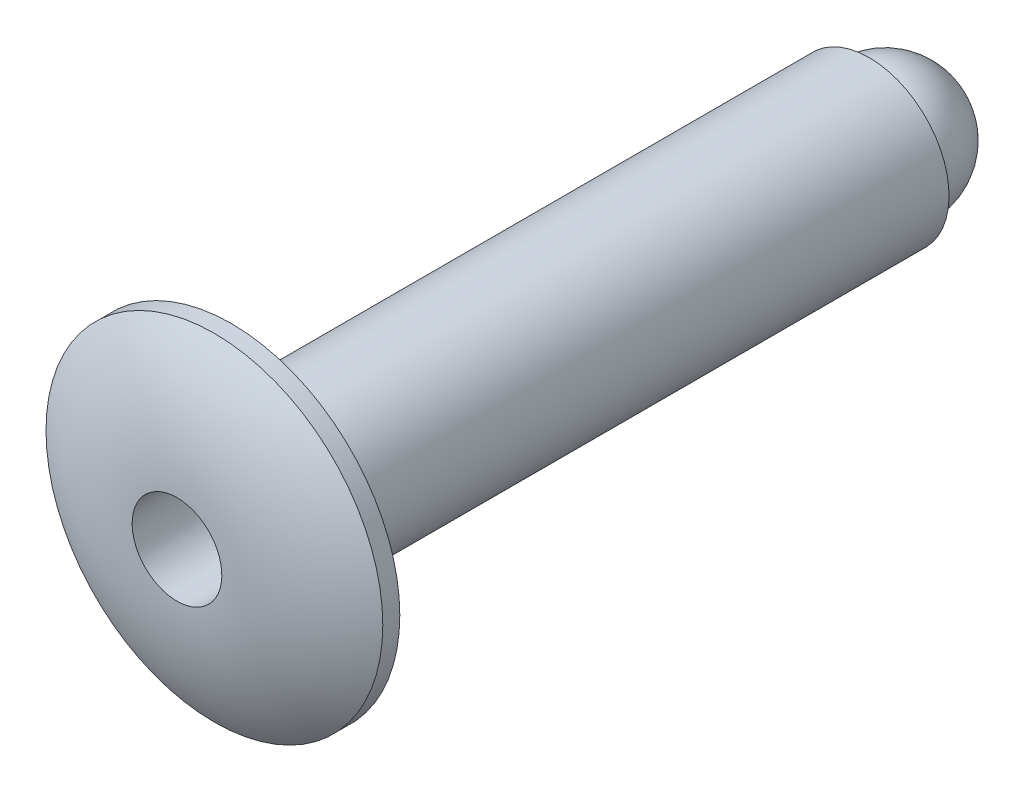
SolidWorks part; units mm, degrees
ref_plane "Front" through (0, 0, 0) normal (0, 0, 1) x (1, 0, 0)
ref_plane "Top" through (0, 0, 0) normal (0, 1, 0) x (1, 0, 0)
ref_plane "Right" through (0, 0, 0) normal (1, 0, 0) x (0, 0, -1)
sketch "Sketch1" plane through (0, 0, 0) normal (1, 0, 0) x (0, 0, -1)
  line L0 (-15.1003, 0) -> (-0.8128, 0) construction
  line L1 (-0.8128, 0) -> (0, 0) construction
  line L2 (0, 0) -> (9.525, 0) construction
  line L3 (9.525, 0) -> (10.7442, 0) construction
  line L8 (0, 2.5146) -> (0, -2.5146) construction
  line L9 (9.525, 1.1906) -> (9.525, -1.1906) construction
  dimension "Length" = 9.525
  dimension "Head Height" = 0.8128
  dimension "D5" = 1.2192
  dimension "D9" = 14.2875
  dimension "Diameter" = 2.3813
  dimension "Head Diameter" = 5.0292
sketch "Sketch2" plane through (0, 0, 0) normal (1, 0, 0) x (0, 0, -1)
  line L0 (-15.1003, 0.5953) -> (-15.1003, 0) construction
  line L1 (-15.1003, 0.5953) -> (0, 0.5953) construction
  line L2 (0, 2.5146) -> (0, -2.5146) construction
  line L3 (0, 0) -> (0, 2.5146) construction
  line L4 (-0.8128, 0) -> (-0.8128, -1.8472) construction
  line L5 (9.525, 1.1906) -> (0, 1.1906)
  line L6 (9.525, 1.1906) -> (9.525, 0) construction
  line L7 (10.7442, 0) -> (10.7442, 1.1906) construction
  line L8 (9.525, 1.1906) -> (9.525, 0)
  line L9 (10.7442, 1.1906) -> (9.525, 1.1906) construction
  line L11 (9.525, 0) -> (10.7442, 0) construction
  line L12 (9.525, 0) -> (0.9525, 0)
  line L13 (-0.8128, 0.5953) -> (-0.8128, 0) construction
  line L14 (9.525, 1.1906) -> (9.525, 0) construction
  line L15 (9.525, 1.1906) -> (9.525, 0) construction
  line L16 (9.525, 0) -> (9.525, 1.1906) construction
  line L17 (9.525, 1.1906) -> (9.525, 0) construction
  line L18 (9.525, 0) -> (9.525, 1.1906) construction
  line L19 (0, 1.1906) -> (0, 2.5146)
  line L20 (-0.8128, 0.6697) -> (0, 0.6697)
  line L21 (-15.1003, 0.6697) -> (0, 0.6697) construction
  line L22 (0, 2.5146) -> (-0.254, 2.5146)
  line L23 (0, 0.6697) -> (0.9525, 0.6697)
  line L24 (0.9525, 0.6697) -> (0.9525, 0)
  arc A0 (10.7442, 0) -> (9.525, 0.9525) centre (9.7625, 0) ccw construction
  arc A2 (-0.254, 2.5146) -> (-0.8128, 0.6697) centre (2.512, 0.6697) ccw
  dimension "D3" = 0.254
  dimension "D1" = 0.5953
  dimension "D2" = 0.9525
  dimension "D5" = 0.9525
  dimension "D4" = 0.0744
revolve "Revolve1" add sketch "Sketch2" angle 360 about L12
sketch "Sketch7" plane through (0, 0, 0) normal (1, 0, 0) x (0, 0, -1)
  line L0 (-15.1003, 0.5953) -> (0.9525, 0.5953)
  line L1 (0.9525, 0.6697) -> (0.9525, 0) construction
  line L2 (0.9525, 0.5953) -> (0.9525, 0)
  line L3 (0.9525, 0) -> (-15.1003, 0)
  line L4 (-15.1003, 0) -> (-15.1003, 0.5953)
revolve "Revolve2" [suppressed] add sketch "Sketch7" angle 360 about L0
sketch "Sketch8" plane through (0, 0, 0) normal (1, 0, 0) x (0, 0, -1)
  line L1 (9.525, 0.9525) -> (9.525, 0)
  line L2 (9.525, 0) -> (10.7442, 0)
  arc A0 (10.7442, 0) -> (9.525, 0.9525) centre (9.7625, 0) ccw construction
  arc A1 (10.7442, 0) -> (9.525, 0.9525) centre (9.7625, 0) ccw
revolve "Revolve3" add sketch "Sketch8" angle 360 about L3
sketch "Sketch3" [suppressed] plane through (0, 0, 0) normal (0, 1, 0) x (1, 0, 0)
  line L0 (-0.7985, -13.2439) -> (-0.387, -15.1003)
  line L2 (-0.5953, -15.1003) -> (0.5953, -15.1003) construction
  line L3 (0, -15.1003) -> (0, -15.6083) construction
  line L4 (-0.387, -15.1003) -> (0.387, -15.1003)
  line L5 (-0.7985, -13.2439) -> (-0.7985, -15.6083)
  line L6 (-0.7985, -15.6083) -> (0.7985, -15.6083)
  line L7 (0.7985, -15.6083) -> (0.7985, -13.2439)
  line L8 (-0.5953, 0.9525) -> (-0.5953, -15.1003) construction
  line L9 (0, -15.1003) -> (0, -0.8128) construction
  line L10 (0.387, -15.1003) -> (0.7985, -13.2439)
  point P12 (0, -15.1003)
  dimension "D3" = 0.508
  dimension "D2" = 0.2032
  dimension "D1" = 25
  dimension "D4" = 0.7739
extrude "Cut-Extrude1" [suppressed] cut sketch "Sketch3" against normal through all both and the other way through all
pattern_circular "CirPattern1" [suppressed] count 2 every 90 about axis through (0, 0, 15.1003) along (0, 0, -1)
sketch "Sketch9" [suppressed] plane through (0, 0, 15.1003) normal (0, 0, 1) x (1, 0, 0)
  line L8 (-0.3616, -0.3616) -> (0.3616, -0.3616)
  line L9 (0.3616, -0.3616) -> (0.3616, 0.3616)
  line L10 (0.3616, 0.3616) -> (-0.3616, 0.3616)
  line L11 (-0.3616, 0.3616) -> (-0.3616, -0.3616)
  line L12 (-0.3616, -0.3616) -> (0.3616, -0.3616)
  line L13 (0.3616, -0.3616) -> (0.3616, 0.3616)
  line L14 (0.3616, 0.3616) -> (-0.3616, 0.3616)
  line L15 (-0.3616, 0.3616) -> (-0.3616, -0.3616)
  dimension "D1" = 0.0254
extrude "Cut-Extrude3" [suppressed] cut sketch "Sketch9" against normal blind 2.54
fillet "Fillet2" radius 0.254 1 edges at (0, 1.1906, 0)
ref_plane "Contact Plane 1" through (0, 0, 0) normal (0, 0, -1) x (-1, 0, 0)
equation "\"D5@Sketch1\" = \"Head Height@Sketch1\" * 1.5"
equation "\"D9@Sketch1\" = \"Length@Sketch1\" * 1.5"
equation "\"D1@Sketch2\"=\"Diameter@Sketch1\"/4"
equation "\"D4@Sketch2\"=\"D1@Sketch2\"/8"
equation "\"D2@Sketch2\"=\"Length@Sketch1\"/10"
equation "\"D4@Sketch3\"=\"D1@Sketch2\"*2*.65"
equation "\"D5@Sketch2\"=\"Diameter@Sketch1\"*.8/2"
